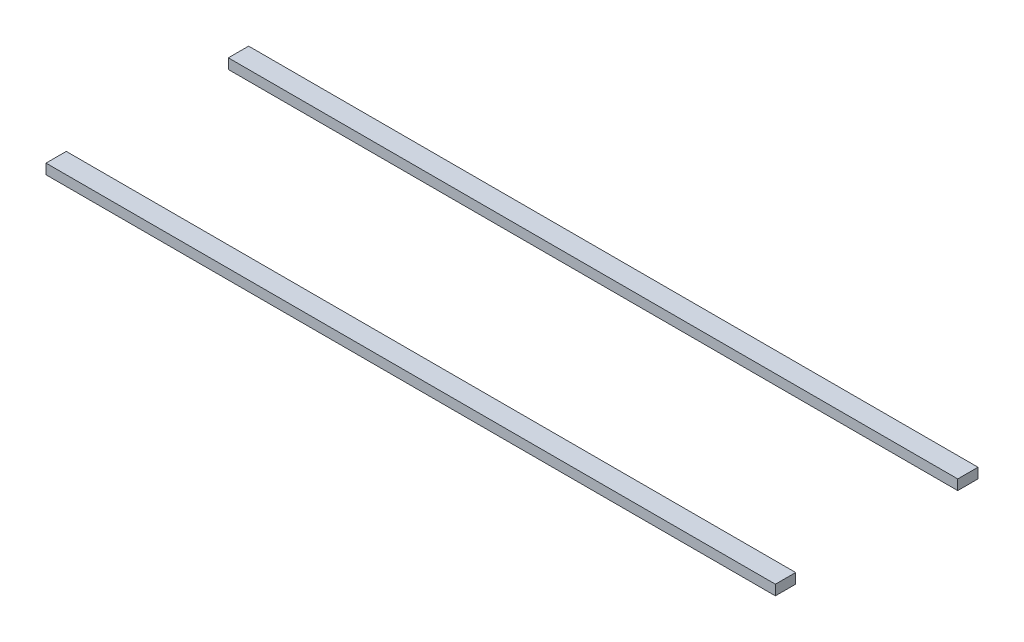
SolidWorks part; units mm, degrees
material "Beech"
ref_plane "Front Plane" through (0, 0, 0) normal (0, 0, 1) x (1, 0, 0)
ref_plane "Top Plane" through (0, 0, 0) normal (0, 1, 0) x (1, 0, 0)
ref_plane "Right Plane" through (0, 0, 0) normal (1, 0, 0) x (0, 0, -1)
sketch "Sketch1" plane through (0, 0, 0) normal (0, 1, 0) x (1, 0, 0)
  line L0 (-137.16, 30.48) -> (137.16, 30.48)
  line L1 (137.16, 38.1) -> (-137.16, 38.1)
  line L2 (137.16, 38.1) -> (137.16, -38.1)
  line L3 (137.16, -38.1) -> (-137.16, -38.1)
  line L4 (-137.16, 38.1) -> (-137.16, -38.1)
  line L5 (137.16, 38.1) -> (-137.16, -38.1) construction
  line L6 (137.16, -38.1) -> (-137.16, 38.1) construction
  line L7 (-137.16, -30.48) -> (137.16, -30.48)
  point P0 (0, 0)
  dimension "D1" = 274.32
  dimension "D2" = 76.2
  dimension "D3" = 7.62
  dimension "D4" = 7.62
extrude "Boss-Extrude1" add sketch "Sketch1" along normal blind 3.81 contours L7 L4 L3 L2 | L1 L4 L0 L2
